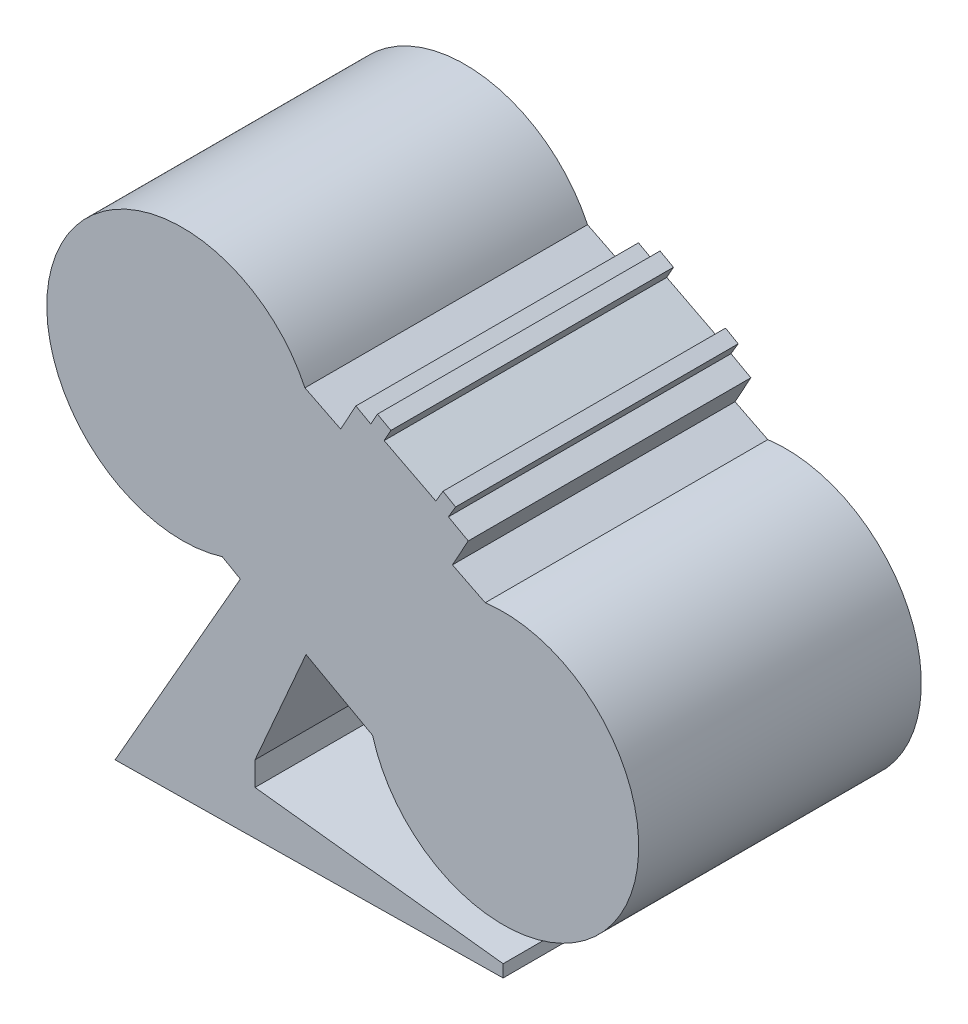
SolidWorks part; units mm, degrees
ref_plane "前视基准面" through (0, 0, 0) normal (0, 0, 1) x (1, 0, 0)
ref_plane "上视基准面" through (0, 0, 0) normal (0, 1, 0) x (1, 0, 0)
ref_plane "右视基准面" through (0, 0, 0) normal (1, 0, 0) x (0, 0, -1)
sketch "草图1" plane through (0, 0, 0) normal (0, 0, 1) x (1, 0, 0)
  line L0 (209.7535, -168.6776) -> (839.0051, -168.6776) construction
  line L1 (0, 0) -> (436.3, 0) construction
  line L2 (0, 0) -> (0, 364.6) construction
  line L3 (0, 364.6) -> (436.3, 364.6) construction
  line L4 (436.3, 0) -> (436.3, 364.6) construction
  line L5 (336.7295, 3.7243) -> (51.1621, 0)
  line L6 (51.1621, 0) -> (143.3173, 161.2984)
  line L7 (143.3173, 161.2984) -> (130.026, 168.8921)
  line L8 (336.7295, 3.7243) -> (336.7295, 12.8261)
  line L9 (336.7295, 12.8261) -> (154.1256, 33.8739)
  line L10 (154.1256, 33.8739) -> (154.1256, 51.5085)
  line L11 (154.1256, 51.5085) -> (191.6703, 137.4063)
  line L12 (191.6703, 137.4063) -> (240.6624, 110.3529)
  line L13 (239.3581, 308.0834) -> (244.2175, 316.8866)
  line L14 (244.2175, 316.8866) -> (254.0986, 311.4323)
  line L15 (254.0986, 311.4323) -> (249.158, 302.4821)
  line L16 (296.4674, 277.5375) -> (301.7069, 286.4363)
  line L17 (301.7069, 286.4363) -> (292.4773, 291.8705)
  line L18 (292.4773, 291.8705) -> (287.2378, 282.9717)
  line L19 (239.3581, 308.0834) -> (228.3508, 314.1595)
  line L20 (228.3508, 314.1595) -> (217.1251, 293.8231)
  line L21 (217.1251, 293.8231) -> (190.8486, 306.9572)
  line L22 (249.158, 302.4821) -> (287.2378, 282.9717)
  line L23 (296.4674, 277.5375) -> (311.0581, 269.4834)
  line L24 (311.0581, 269.4834) -> (299.4185, 248.3971)
  line L25 (299.4185, 248.3971) -> (323.5488, 236.3357)
  circle A0 centre (100.6528, 264.2619) radius 99.7906
  circle A1 centre (336.7295, 137.4063) radius 99.8036
  dimension "D1" = 436.3
  dimension "D2" = 364.6
extrude "凸台-拉伸1" add sketch "草图1" along normal blind 208 contours A0 | A1 L25 L24 L23 L16 L17 L18 L22 L15 L14 L13 L19 L20 L21 A0 L7 L6 L5 L8 L9 L10 L11 L12 | A1
